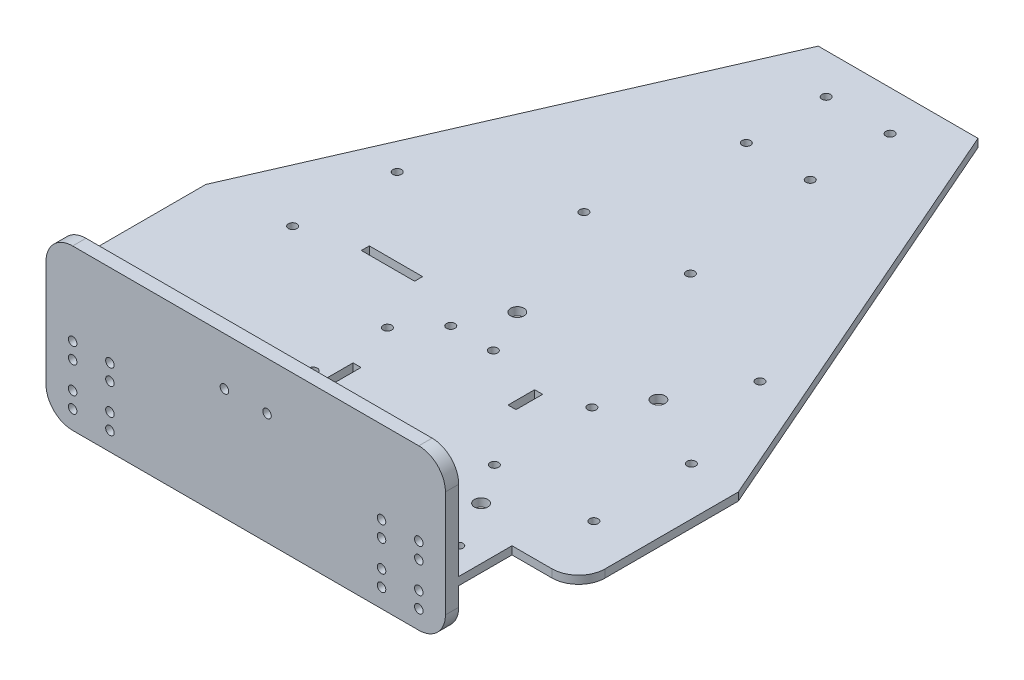
SolidWorks part; units mm, degrees
ref_plane "Front Plane" through (0, 0, 0) normal (0, 0, 1) x (1, 0, 0)
ref_plane "Top Plane" through (0, 0, 0) normal (0, 1, 0) x (1, 0, 0)
ref_plane "Right Plane" through (0, 0, 0) normal (1, 0, 0) x (0, 0, -1)
sketch "Sketch1" plane through (0, 0, 0) normal (0, 1, 0) x (1, 0, 0)
  line L8 (100, -40) -> (100, 10)
  line L10 (-30, 170) -> (30, 170)
  line L11 (30, 170) -> (100, 10)
  line L12 (-30, 170) -> (-100, 10)
  line L13 (-100, -40) -> (-100, 10)
  line L18 (75, -50) -> (90, -50)
  line L20 (-75, -50) -> (-90, -50)
  line L32 (-75, -50) -> (-75, -70)
  line L33 (-75, -70) -> (75, -70)
  line L34 (75, -70) -> (75, -50)
  arc A6 (90, -50) -> (100, -40) centre (90, -40) ccw
  arc A7 (-90, -50) -> (-100, -40) centre (-90, -40) cw
  point P24 (-100, -70)
  dimension "D3" = 20
  dimension "D1" = 60
  dimension "D2" = 200
  dimension "D4" = 25
  dimension "D5" = 25
  dimension "D9" = 70
  dimension "D12" = 160
extrude "Boss-Extrude1" add sketch "Sketch1" along normal blind 3
sketch "Sketch3" plane through (0, 3, 0) normal (0, 1, 0) x (1, 0, 0)
  line L0 (-19.321, -35.0624) -> (-19.321, -40.0624) construction
  line L1 (-19.321, -40.0624) -> (-29.321, -40.0624) construction
  line L2 (-19.321, 12.7376) -> (-19.321, 17.7376) construction
  line L11 (-19.321, 17.7376) -> (-29.321, 17.7376) construction
  line L12 (-70.121, 12.7376) -> (-19.321, 12.7376) construction
  line L13 (-19.321, 12.7376) -> (-19.321, -2.4624) construction
  line L14 (-19.321, -2.4624) -> (-19.321, -30.3624) construction
  line L15 (-19.321, -30.3624) -> (-19.321, -35.0624) construction
  line L16 (-19.321, -35.0624) -> (-71.221, -35.0624) construction
  line L17 (-71.221, -35.0624) -> (-70.121, -35.0624) construction
  line L18 (-70.121, -35.0624) -> (-70.121, 12.7376) construction
  line L19 (-19.321, -30.3624) -> (-14.321, -30.3624) construction
  line L20 (-29.321, -40.0624) -> (-49.321, -40.0624)
  line L21 (-29.321, -40.0624) -> (-29.321, -43.0624)
  line L22 (-29.321, -43.0624) -> (-49.321, -43.0624)
  line L23 (-49.321, -40.0624) -> (-49.321, -43.0624)
  line L24 (-29.321, 17.7376) -> (-49.321, 17.7376)
  line L25 (-29.321, 17.7376) -> (-29.321, 20.7376)
  line L26 (-29.321, 20.7376) -> (-49.321, 20.7376)
  line L27 (-49.321, 17.7376) -> (-49.321, 20.7376)
  line L29 (-14.321, -30.3624) -> (-11.321, -30.3624)
  line L30 (-14.321, -30.3624) -> (-14.321, -20.3624)
  line L31 (-14.321, -20.3624) -> (-11.321, -20.3624)
  line L32 (-11.321, -30.3624) -> (-11.321, -20.3624)
  circle A4 centre (-70.121, 12.7376) radius 1.6
  circle A5 centre (-71.221, -35.0624) radius 1.6
  circle A6 centre (-19.321, -2.4624) radius 1.6
  circle A7 centre (-19.321, -30.3624) radius 1.6
  dimension "D8" = 10
  dimension "D9" = 3
  dimension "D10" = 10
  dimension "D11" = 20
  dimension "D21" = 3.2
  dimension "D22" = 3.2
  dimension "D23" = 3.2
  dimension "D24" = 3.2
  dimension "D3" = 27.9
  dimension "D4" = 15.2
  dimension "D5" = 4.7
  dimension "D6" = 5
  dimension "D7" = 5
  dimension "D12" = 3
  dimension "D13" = 20
  dimension "D14" = 5
  dimension "D15" = 50.8
  dimension "D16" = 10
  dimension "D17" = 3
  dimension "D19" = 51.9
  dimension "D20" = 1.1
extrude "arduino" cut sketch "Sketch3" against normal through all
sketch "Sketch6" plane through (0, 3, 0) normal (0, 1, 0) x (1, 0, 0)
  line L0 (0, 170) -> (0, 140) construction
  line L2 (30, 170) -> (-30, 170) construction
  line L3 (-12, 155) -> (12, 155) construction
  line L4 (-12, 155) -> (-12, 125) construction
  line L5 (-12, 125) -> (12, 125) construction
  line L6 (12, 155) -> (12, 125) construction
  line L7 (-12, 155) -> (12, 125) construction
  line L8 (-12, 125) -> (12, 155) construction
  circle A0 centre (12, 155) radius 1.6
  circle A1 centre (-12, 155) radius 1.6
  circle A2 centre (12, 125) radius 1.6
  circle A3 centre (-12, 125) radius 1.6
  dimension "D4" = 3.2
  dimension "D5" = 3.2
  dimension "D6" = 3.2
  dimension "D7" = 3.2
  dimension "D1" = 30
  dimension "D2" = 30
  dimension "D3" = 24
extrude "Cut-Extrude4" cut sketch "Sketch6" against normal through all
sketch "Sketch8" plane through (0, 3, 0) normal (0, 1, 0) x (1, 0, 0)
  line L0 (-75, -50) -> (-75, -60) construction
  line L5 (-100, 10) -> (100, 10) construction
  line L6 (-75, -50) -> (-75, -70) construction
  line L7 (0, 10) -> (8, 10) construction
  line L12 (-75, -60) -> (-65, -60) construction
  circle A16 centre (8, 10) radius 1.6
  circle A17 centre (-8, 10) radius 1.6
  circle A22 centre (-65, -60) radius 1.6
  circle A23 centre (65, -60) radius 1.6
  dimension "D6" = 8
  dimension "D7" = 3.2
  dimension "D2" = 3.2
  dimension "D1" = 10
extrude "Cut-Extrude5" cut sketch "Sketch8" against normal blind 10
sketch "Sketch9" plane through (0, 3, 0) normal (0, 1, 0) x (1, 0, 0)
  line L0 (0, 72) -> (20, 72) construction
  line L1 (81.9982, 10.3676) -> (82.3658, -26.6306) construction
  line L2 (45.3676, -26.9982) -> (82.3658, -26.6306) construction
  line L4 (-100, 10) -> (-100, 60) construction
  line L5 (-100, 60) -> (-68.125, 60) construction
  line L6 (0, 72) -> (-20, 72) construction
  line L10 (45, 10) -> (45.3676, -26.9982) construction
  line L11 (45, 10) -> (81.9982, 10.3676) construction
  line L12 (-68.125, 60) -> (-68.125, 50) construction
  line L13 (0, -55) -> (0, 55) construction
  line L14 (45, 10) -> (45, 25) construction
  line L15 (45, 25) -> (55, 25) construction
  line L16 (45.3676, -26.9982) -> (45.3676, -41.9982) construction
  line L17 (45.3676, -41.9982) -> (55.3676, -41.9982) construction
  line L18 (45, 10) -> (30, 10) construction
  line L19 (30, 10) -> (30, 0) construction
  line L20 (0, 72) -> (0, 27) construction
  line L25 (28.5, 5) -> (31.5, 5)
  line L26 (28.5, 5) -> (28.5, -5)
  line L27 (28.5, -5) -> (31.5, -5)
  line L28 (31.5, 5) -> (31.5, -5)
  line L29 (28.5, 5) -> (31.5, -5) construction
  line L30 (28.5, -5) -> (31.5, 5) construction
  circle A12 centre (20, 72) radius 1.6
  circle A13 centre (-20, 72) radius 1.6
  circle A14 centre (45, 10) radius 1.6
  circle A15 centre (81.9982, 10.3676) radius 1.6
  circle A16 centre (82.3658, -26.6306) radius 1.6
  circle A17 centre (45.3676, -26.9982) radius 1.6
  circle A18 centre (-68.125, 50) radius 1.6
  circle A19 centre (68.125, 50) radius 1.6
  circle A20 centre (55, 25) radius 2.5
  circle A21 centre (55.3676, -41.9982) radius 2.5
  circle A22 centre (0, 27) radius 2.5
  dimension "D3" = 3.2
  dimension "D4" = 3.2
  dimension "D5" = 50
  dimension "D7" = 3.2
  dimension "D8" = 3.2
  dimension "D9" = 3.2
  dimension "D10" = 3.2
  dimension "D12" = 10
  dimension "D13" = 3.2
  dimension "D16" = 5
  dimension "D19" = 5
  dimension "D24" = 5
  dimension "D1" = 20
  dimension "D2" = 20
  dimension "D6" = 31.875
  dimension "D11" = 37
  dimension "D14" = 15
  dimension "D15" = 10
  dimension "D17" = 15
  dimension "D18" = 10
  dimension "D20" = 15
  dimension "D21" = 10
  dimension "D22" = 3
  dimension "D23" = 45
extrude "l298n" cut sketch "Sketch9" against normal blind 10
ref_point "bottomofcart"
ref_plane "Plane1" through (0, 43, 0) normal (0, 1, 0) x (1, 0, 0)
sketch "Sketch11" plane through (0, 43, 0) normal (0, 1, 0) x (1, 0, 0)
  line L1 (-75, -70) -> (75, -70)
  line L2 (-75, -70) -> (-75, -75)
  line L3 (-75, -75) -> (75, -75)
  line L4 (75, -70) -> (75, -75)
  dimension "D1" = 5
  dimension "D2" = 150
extrude "Boss-Extrude3" add sketch "Sketch11" against normal blind 60
fillet "Fillet1" radius 10 4 edges at (75, -17, 72.5) (75, 43, 72.5) (-75, -17, 72.5) (-75, 43, 72.5)
sketch "Sketch12" plane through (0, 0, 75) normal (0, 0, 1) x (1, 0, 0)
  line L0 (-65, -17) -> (-65, -10) construction
  line L1 (-65, -10) -> (-51, -10) construction
  line L2 (-65, -10) -> (-65, -4) construction
  line L3 (-65, -4) -> (-65, 6) construction
  line L4 (-65, 6) -> (-65, 12) construction
  line L5 (0, -33) -> (0, 33) construction
  line L6 (0, 43) -> (0, 25) construction
  line L7 (-65, 43) -> (65, 43) construction
  line L8 (0, 25) -> (-8, 25) construction
  circle A0 centre (-65, -10) radius 1.6
  circle A1 centre (-51, -10) radius 1.6
  circle A2 centre (-65, -4) radius 1.6
  circle A3 centre (-65, 6) radius 1.6
  circle A4 centre (-65, 12) radius 1.6
  circle A5 centre (-51, 12) radius 1.6
  circle A6 centre (-51, 6) radius 1.6
  circle A7 centre (-51, -4) radius 1.6
  circle A8 centre (51, -10) radius 1.6
  circle A9 centre (65, -10) radius 1.6
  circle A10 centre (51, -4) radius 1.6
  circle A11 centre (51, 6) radius 1.6
  circle A12 centre (51, 12) radius 1.6
  circle A13 centre (65, -4) radius 1.6
  circle A14 centre (65, 6) radius 1.6
  circle A15 centre (65, 12) radius 1.6
  circle A16 centre (-8, 25) radius 1.6
  circle A17 centre (8, 25) radius 1.6
  dimension "D2" = 3.2
  dimension "D3" = 14
  dimension "D4" = 3.2
  dimension "D6" = 3.2
  dimension "D9" = 3.2
  dimension "D10" = 3.2
  dimension "D14" = 3.2
  dimension "D1" = 7
  dimension "D5" = 6
  dimension "D7" = 10
  dimension "D8" = 6
  dimension "D12" = 18
  dimension "D13" = 8
  dimension "D11" = 2
extrude "Cut-Extrude6" cut sketch "Sketch12" against normal blind 10
